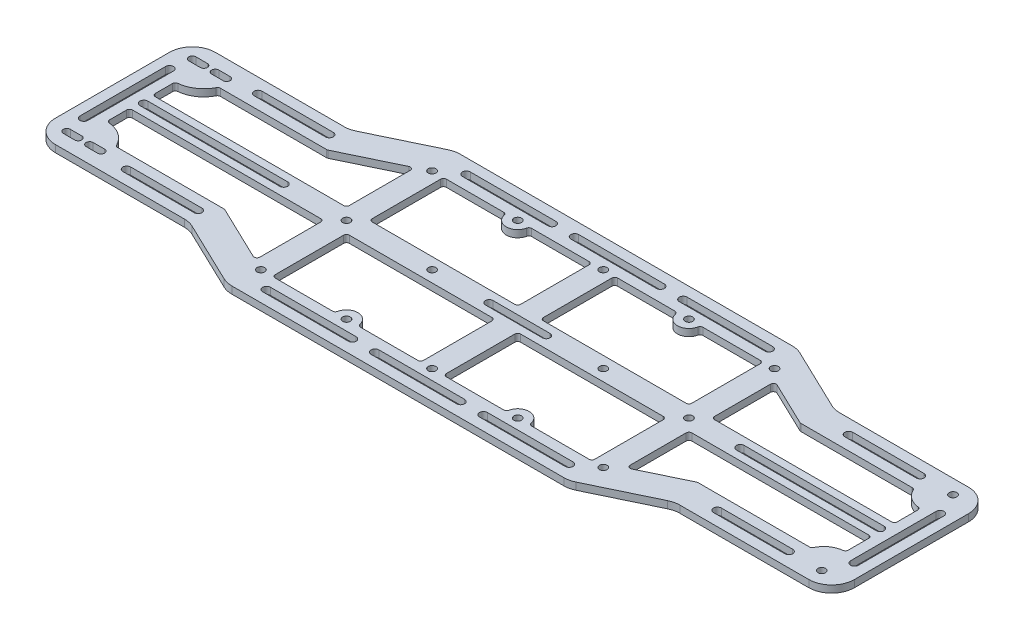
SolidWorks part; units mm, degrees
material "6061-T6 (SS)"
ref_plane "Front Plane" through (0, 0, 0) normal (0, 0, 1) x (1, 0, 0)
ref_plane "Top Plane" through (0, 0, 0) normal (0, 1, 0) x (1, 0, 0)
ref_plane "Right Plane" through (0, 0, 0) normal (1, 0, 0) x (0, 0, -1)
sketch "Sketch1" plane through (0, 0, 0) normal (0, 1, 0) x (1, 0, 0)
  line L1 (0, 0) -> (355.6, 0)
  line L2 (0, 0) -> (0, 101.6)
  line L3 (0, 101.6) -> (355.6, 101.6)
  line L4 (355.6, 0) -> (355.6, 101.6)
  dimension "D1" = 355.6
  dimension "D2" = 101.6
extrude "Boss-Extrude1" add sketch "Sketch1" along normal blind 3.175
sketch "Sketch2" plane through (0, 0, 0) normal (0, -1, 0) x (1, 0, 0)
  line L0 (0, -50.8) -> (355.6, -50.8) construction
  line L1 (0, -101.6) -> (0, 0) construction
  line L2 (355.6, 0) -> (355.6, -101.6) construction
  point P6 (10.16, -22.86)
  point P7 (344.8634, -21.59)
  point P8 (344.8634, -80.01)
  point P9 (10.16, -78.74)
  dimension "D1" = 55.88
  dimension "D2" = 58.42
  dimension "D3" = 334.7034
  dimension "D4" = 10.16
hole_wizard "M3 Clearance Hole2" positions "Sketch6" profile "Sketch5" hole size "M3" standard "ANSI Metric" end condition through all
sketch "Sketch6" plane through (0, 0, 0) normal (0, -1, 0) x (-1, 0, 0)
  point P0 (-344.8634, 21.59)
  point P3 (-344.8634, 80.01)
sketch "Sketch5" plane through (344.8634, 0, -21.59) normal (1, 0, 0) x (0, 0, -1)
  line L0 (0, 0) -> (0, 3.175)
  line L1 (0, 3.175) -> (1.7, 3.175)
  line L2 (1.7, 3.175) -> (1.7, 0)
  line L5 (1.7, 0) -> (0, 0)
  line L11 (0, -6.35) -> (0, 107.95) construction
  dimension "Thru Hole Dia." = 3.4
  dimension "Thru Hole Depth" = 3.175
sketch "Sketch7" plane through (0, 0, 0) normal (0, -1, 0) x (1, 0, 0)
  line L0 (7.62, -22.86) -> (12.7, -22.86) construction
  line L1 (7.62, -21.2838) -> (12.7, -21.2838)
  line L2 (7.62, -24.4362) -> (12.7, -24.4362)
  line L3 (0, -50.8) -> (34.1188, -50.8) construction
  line L4 (0, -50.8) -> (355.6, -50.8) construction
  line L5 (7.62, -78.74) -> (12.7, -78.74) construction
  line L6 (7.62, -80.3162) -> (12.7, -80.3162)
  line L7 (7.62, -77.1638) -> (12.7, -77.1638)
  arc A0 (7.62, -21.2838) -> (7.62, -24.4362) centre (7.62, -22.86) ccw
  arc A1 (12.7, -24.4362) -> (12.7, -21.2838) centre (12.7, -22.86) ccw
  arc A2 (7.62, -80.3162) -> (7.62, -77.1638) centre (7.62, -78.74) cw
  arc A3 (12.7, -77.1638) -> (12.7, -80.3162) centre (12.7, -78.74) cw
  point P2 (10.16, -22.86)
  point P15 (10.16, -78.74)
  dimension "D1" = 1.5762
  dimension "D2" = 5.08
extrude "Cut-Extrude1" cut sketch "Sketch7" against normal through all
sketch "Sketch16" plane through (0, 3.175, 0) normal (0, 1, 0) x (1, 0, 0)
  line L0 (355.6, 15.24) -> (285.75, 15.24)
  line L1 (355.6, 0) -> (355.6, 101.6) construction
  line L2 (0, 0) -> (355.6, 0) construction
  line L3 (355.6, 15.24) -> (355.6, 0)
  line L4 (355.6, 0) -> (254, 0)
  line L5 (285.75, 15.24) -> (254, 0)
  line L6 (355.6, 50.8) -> (0, 50.8) construction
  line L7 (0, 101.6) -> (0, 0) construction
  line L8 (177.8, 0) -> (177.8, 101.6) construction
  line L9 (355.6, 101.6) -> (0, 101.6) construction
  line L10 (69.85, 15.24) -> (101.6, 0)
  line L11 (0, 0) -> (101.6, 0)
  line L12 (0, 15.24) -> (0, 0)
  line L13 (0, 15.24) -> (69.85, 15.24)
  line L14 (0, 86.36) -> (69.85, 86.36)
  line L15 (0, 86.36) -> (0, 101.6)
  line L16 (0, 101.6) -> (101.6, 101.6)
  line L17 (69.85, 86.36) -> (101.6, 101.6)
  line L18 (285.75, 86.36) -> (254, 101.6)
  line L19 (355.6, 101.6) -> (254, 101.6)
  line L20 (355.6, 86.36) -> (355.6, 101.6)
  line L21 (355.6, 86.36) -> (285.75, 86.36)
  dimension "D1" = 15.24
  dimension "D2" = 101.6
  dimension "D3" = 69.85
extrude "Cut-Extrude3" cut sketch "Sketch16" against normal through all
fillet "Fillet1" radius 10.16 12 edges at (0, 1.5875, -86.36) (69.85, 1.5875, -86.36) (101.6, 1.5875, -101.6) (254, 1.5875, -101.6) (285.75, 1.5875, -86.36) (355.6, 1.5875, -86.36) (0, 1.5875, -15.24) (69.85, 1.5875, -15.24) (101.6, 1.5875, 0) (254, 1.5875, 0) (285.75, 1.5875, -15.24) (355.6, 1.5875, -15.24)
sketch "Sketch17" plane through (0, 3.175, 0) normal (0, 1, 0) x (1, 0, 0)
  line L0 (0, 50.8) -> (355.6, 50.8) construction
  line L1 (142.24, 88.9) -> (104.14, 50.8) construction
  line L2 (0, 50.8) -> (355.6, 50.8) construction
  line L3 (0, 76.2) -> (0, 25.4) construction
  line L4 (111.76, 88.9) -> (78.74, 55.88)
  line L5 (78.74, 55.88) -> (104.14, 55.88)
  line L6 (104.14, 55.88) -> (137.16, 88.9)
  line L7 (137.16, 88.9) -> (111.76, 88.9)
  line L8 (104.14, 88.9) -> (142.24, 88.9) construction
  line L9 (78.74, 45.72) -> (104.14, 45.72)
  line L10 (104.14, 45.72) -> (137.16, 12.7)
  line L11 (137.16, 12.7) -> (111.76, 12.7)
  line L12 (111.76, 12.7) -> (78.74, 45.72)
  line L13 (175.26, 88.9) -> (149.86, 88.9)
  line L14 (149.86, 88.9) -> (116.84, 55.88)
  line L15 (142.24, 55.88) -> (175.26, 88.9)
  line L16 (116.84, 55.88) -> (142.24, 55.88)
  line L17 (116.84, 45.72) -> (142.24, 45.72)
  line L18 (142.24, 45.72) -> (175.26, 12.7)
  line L19 (149.86, 12.7) -> (116.84, 45.72)
  line L20 (175.26, 12.7) -> (149.86, 12.7)
  line L21 (213.36, 88.9) -> (187.96, 88.9)
  line L22 (187.96, 88.9) -> (154.94, 55.88)
  line L23 (180.34, 55.88) -> (213.36, 88.9)
  line L24 (154.94, 55.88) -> (180.34, 55.88)
  line L25 (154.94, 45.72) -> (180.34, 45.72)
  line L26 (180.34, 45.72) -> (213.36, 12.7)
  line L27 (187.96, 12.7) -> (154.94, 45.72)
  line L28 (213.36, 12.7) -> (187.96, 12.7)
  line L29 (251.46, 88.9) -> (226.06, 88.9)
  line L30 (226.06, 88.9) -> (193.04, 55.88)
  line L31 (218.44, 55.88) -> (251.46, 88.9)
  line L32 (193.04, 55.88) -> (218.44, 55.88)
  line L33 (193.04, 45.72) -> (218.44, 45.72)
  line L34 (218.44, 45.72) -> (251.46, 12.7)
  line L35 (226.06, 12.7) -> (193.04, 45.72)
  line L36 (251.46, 12.7) -> (226.06, 12.7)
  line L37 (260.0411, 84.7811) -> (231.14, 55.88)
  line L38 (231.14, 55.88) -> (256.54, 55.88)
  line L39 (256.54, 55.88) -> (277.2032, 76.5432)
  line L40 (277.2032, 76.5432) -> (260.0411, 84.7811)
  line L41 (256.0844, 100.5995) -> (283.6656, 87.3605) construction
  line L42 (231.14, 45.72) -> (256.54, 45.72)
  line L43 (260.0411, 16.8189) -> (231.14, 45.72)
  line L44 (256.54, 45.72) -> (277.2032, 25.0568)
  line L45 (277.2032, 25.0568) -> (260.0411, 16.8189)
  line L46 (287.02, 73.66) -> (269.24, 55.88)
  line L47 (269.24, 55.88) -> (342.9, 55.88)
  line L48 (342.9, 55.88) -> (342.9, 67.4627)
  line L49 (287.02, 73.66) -> (333.8649, 73.66)
  line L51 (288.0621, 86.36) -> (345.44, 86.36) construction
  line L52 (355.6, 25.4) -> (355.6, 76.2) construction
  line L53 (269.24, 45.72) -> (342.9, 45.72)
  line L54 (342.9, 45.72) -> (342.9, 34.1373)
  line L55 (287.02, 27.94) -> (333.8649, 27.94)
  line L56 (287.02, 27.94) -> (269.24, 45.72)
  line L57 (12.7, 55.88) -> (66.04, 55.88)
  line L58 (66.04, 55.88) -> (86.36, 76.2)
  line L59 (72.7401, 73.66) -> (24.3397, 73.66)
  line L60 (12.7, 66.04) -> (12.7, 55.88)
  line L61 (10.16, 86.36) -> (67.5379, 86.36) construction
  line L62 (86.36, 76.2) -> (94.0476, 83.8876)
  line L63 (94.0476, 83.8876) -> (72.7401, 73.66)
  line L64 (71.9344, 87.3605) -> (99.5156, 100.5995) construction
  line L65 (12.7, 45.72) -> (66.04, 45.72)
  line L66 (86.36, 25.4) -> (94.0476, 17.7124)
  line L67 (66.04, 45.72) -> (86.36, 25.4)
  line L68 (94.0476, 17.7124) -> (72.7401, 27.94)
  line L69 (72.7401, 27.94) -> (24.3397, 27.94)
  line L70 (12.7, 35.56) -> (12.7, 45.72)
  arc A0 (342.9, 67.4627) -> (333.8649, 73.66) centre (344.8634, 80.01) cw
  circle A1 centre (344.8634, 80.01) radius 1.7 construction
  arc A2 (342.9, 34.1373) -> (333.8649, 27.94) centre (344.8634, 21.59) ccw
  arc A3 (24.3397, 73.66) -> (12.7, 66.04) centre (12.7, 78.74) cw
  arc A4 (12.7, 77.1638) -> (12.7, 80.3162) centre (12.7, 78.74) ccw construction
  arc A5 (24.3397, 27.94) -> (12.7, 35.56) centre (12.7, 22.86) ccw
  point P4 (104.14, 88.9)
  point P8 (104.14, 50.8)
  point P9 (104.14, 12.7)
  point P12 (142.24, 88.9)
  point P13 (142.24, 50.8)
  point P14 (142.24, 12.7)
  point P15 (180.34, 88.9)
  point P16 (180.34, 50.8)
  point P17 (180.34, 12.7)
  point P18 (218.44, 88.9)
  point P19 (218.44, 50.8)
  point P20 (218.44, 12.7)
  point P21 (256.54, 88.9)
  point P22 (256.54, 50.8)
  point P23 (256.54, 12.7)
  dimension "D13" = 12.7
  dimension "D17" = 12.7
  dimension "D1" = 38.1
  dimension "D2" = 104.14
  dimension "D4" = 45
  dimension "D5" = 5.08
  dimension "D6" = 25.4
  dimension "D7" = 7.62
  dimension "D9" = 38.1
  dimension "D10" = 38.1
  dimension "D11" = 12.7
  dimension "D12" = 12.7
  dimension "D14" = 12.7
  dimension "D15" = 12.7
  dimension "D16" = 38.1
  dimension "D18" = 12.7
  dimension "D19" = 38.1
  dimension "D3" = 5
  dimension "D8" = 4
hole_wizard "M3 Clearance Hole5" positions "Sketch19" profile "Sketch18" hole size "M3" standard "ANSI Metric" end condition through all
sketch "Sketch19" plane through (0, 3.175, 0) normal (0, 1, 0) x (1, 0, 0)
  point P0 (104.14, 88.9)
  point P3 (142.24, 88.9)
  point P6 (180.34, 88.9)
  point P9 (218.44, 88.9)
  point P12 (256.54, 88.9)
  point P15 (256.54, 12.7)
  point P18 (218.44, 12.7)
  point P21 (180.34, 12.7)
  point P24 (142.24, 12.7)
  point P27 (104.14, 12.7)
  point P30 (104.14, 50.8)
  point P33 (256.54, 50.8)
  point P36 (142.24, 50.8)
  point P39 (180.34, 50.8)
  point P42 (218.44, 50.8)
sketch "Sketch18" plane through (104.14, 3.175, -88.9) normal (1, 0, 0) x (0, 0, 1)
  line L0 (0, 0) -> (0, 3.175)
  line L1 (0, 3.175) -> (1.7, 3.175)
  line L2 (1.7, 3.175) -> (1.7, 0)
  line L5 (1.7, 0) -> (0, 0)
  line L11 (0, -6.35) -> (0, 107.95) construction
  dimension "Thru Hole Dia." = 3.4
  dimension "Thru Hole Depth" = 3.175
sketch "Sketch20" plane through (0, 3.175, 0) normal (0, 1, 0) x (1, 0, 0)
  line L0 (167.64, 50.8) -> (193.04, 50.8) construction
  line L1 (0, 50.8) -> (355.6, 50.8) construction
  line L2 (167.64, 52.5) -> (193.04, 52.5)
  line L3 (167.64, 49.1) -> (193.04, 49.1)
  arc A0 (167.64, 52.5) -> (167.64, 49.1) centre (167.64, 50.8) ccw
  arc A1 (193.04, 49.1) -> (193.04, 52.5) centre (193.04, 50.8) ccw
  circle A2 centre (180.34, 50.8) radius 1.7 construction
  point P5 (180.34, 50.8)
  dimension "D1" = 25.4
extrude "Cut-Extrude5" cut sketch "Sketch20" against normal through all
pattern_linear "LPattern1" count 2 spacing 10.16 along (1, 0, 0) of "Cut-Extrude1"
sketch "Sketch22" plane through (0, 3.175, 0) normal (0, 1, 0) x (1, 0, 0)
  line L0 (13.97, 50.8) -> (76.2, 50.8) construction
  line L1 (0, 50.8) -> (355.6, 50.8) construction
  line L2 (13.97, 52.55) -> (76.2, 52.55)
  line L3 (13.97, 49.05) -> (76.2, 49.05)
  line L4 (0, 76.2) -> (0, 25.4) construction
  arc A0 (13.97, 52.55) -> (13.97, 49.05) centre (13.97, 50.8) ccw
  arc A1 (76.2, 49.05) -> (76.2, 52.55) centre (76.2, 50.8) ccw
  point P4 (45.085, 50.8)
  dimension "D3" = 76.2
  dimension "D1" = 3.5
  dimension "D2" = 13.97
extrude "Cut-Extrude6" cut sketch "Sketch22" against normal through all
sketch "Sketch23" plane through (0, 3.175, 0) normal (0, 1, 0) x (1, 0, 0)
  line L0 (279.4, 50.8) -> (341.63, 50.8) construction
  line L1 (0, 50.8) -> (355.6, 50.8) construction
  line L2 (279.4, 52.55) -> (341.63, 52.55)
  line L3 (279.4, 49.05) -> (341.63, 49.05)
  line L4 (355.6, 25.4) -> (355.6, 76.2) construction
  arc A0 (279.4, 52.55) -> (279.4, 49.05) centre (279.4, 50.8) ccw
  arc A1 (341.63, 49.05) -> (341.63, 52.55) centre (341.63, 50.8) ccw
  point P4 (310.515, 50.8)
  dimension "D2" = 13.97
  dimension "D3" = 76.2
  dimension "D1" = 3.5
extrude "Cut-Extrude7" cut sketch "Sketch23" against normal through all
sketch "Sketch24" plane through (0, 3.175, 0) normal (0, 1, 0) x (1, 0, 0)
  line L0 (6.35, 69.85) -> (6.35, 31.75) construction
  line L1 (0, 50.8) -> (355.6, 50.8) construction
  line L2 (8.1, 69.85) -> (8.1, 31.75)
  line L3 (4.6, 69.85) -> (4.6, 31.75)
  line L4 (349.25, 69.85) -> (349.25, 31.75) construction
  line L5 (351, 69.85) -> (351, 31.75)
  line L6 (347.5, 69.85) -> (347.5, 31.75)
  line L7 (0, 76.2) -> (0, 25.4) construction
  line L8 (355.6, 25.4) -> (355.6, 76.2) construction
  arc A0 (8.1, 69.85) -> (4.6, 69.85) centre (6.35, 69.85) ccw
  arc A1 (4.6, 31.75) -> (8.1, 31.75) centre (6.35, 31.75) ccw
  arc A2 (351, 69.85) -> (347.5, 69.85) centre (349.25, 69.85) ccw
  arc A3 (347.5, 31.75) -> (351, 31.75) centre (349.25, 31.75) ccw
  point P4 (6.35, 50.8)
  point P10 (349.25, 50.8)
  dimension "D1" = 3.5
  dimension "D2" = 38.1
  dimension "D3" = 6.35
  dimension "D4" = 6.35
extrude "Cut-Extrude8" cut sketch "Sketch24" against normal through all
sketch "Sketch25" plane through (0, 3.175, 0) normal (0, 1, 0) x (1, 0, 0)
  line L0 (101.3472, 95.25) -> (256.2857, 95.25) construction
  line L1 (251.6879, 101.6) -> (103.9121, 101.6) construction
  line L2 (113.03, 95.25) -> (151.13, 95.25) construction
  line L3 (113.03, 97) -> (151.13, 97)
  line L4 (113.03, 93.5) -> (151.13, 93.5)
  line L5 (161.29, 95.25) -> (199.39, 95.25) construction
  line L6 (161.29, 97) -> (199.39, 97)
  line L7 (161.29, 93.5) -> (199.39, 93.5)
  line L8 (209.55, 95.25) -> (247.65, 95.25) construction
  line L9 (209.55, 97) -> (247.65, 97)
  line L10 (209.55, 93.5) -> (247.65, 93.5)
  line L11 (0, 76.2) -> (0, 25.4) construction
  arc A0 (113.03, 97) -> (113.03, 93.5) centre (113.03, 95.25) ccw
  arc A1 (151.13, 93.5) -> (151.13, 97) centre (151.13, 95.25) ccw
  arc A2 (161.29, 97) -> (161.29, 93.5) centre (161.29, 95.25) ccw
  arc A3 (199.39, 93.5) -> (199.39, 97) centre (199.39, 95.25) ccw
  arc A4 (209.55, 97) -> (209.55, 93.5) centre (209.55, 95.25) ccw
  arc A5 (247.65, 93.5) -> (247.65, 97) centre (247.65, 95.25) ccw
  point P6 (132.08, 95.25)
  point P11 (180.34, 95.25)
  point P18 (228.6, 95.25)
  dimension "D3" = 10.16
  dimension "D4" = 10.16
  dimension "D5" = 113.03
  dimension "D1" = 6.35
  dimension "D2" = 38.1
  dimension "D6" = 3.5
extrude "Cut-Extrude9" cut sketch "Sketch25" against normal through all
ref_plane "Plane1" through (0, 0, -50.8) normal (0, 0, -1) x (-1, 0, 0)
mirror "Mirror1" about plane through (0, 0, -50.8) normal (0, 0, -1) of "Cut-Extrude9"
sketch "Sketch26" plane through (0, 3.175, 0) normal (0, 1, 0) x (1, 0, 0)
  line L0 (26.8574, 80.01) -> (337.2378, 80.01) construction
  line L1 (35.56, 80.01) -> (67.31, 80.01) construction
  line L2 (35.56, 81.76) -> (67.31, 81.76)
  line L3 (35.56, 78.26) -> (67.31, 78.26)
  line L4 (298.45, 80.01) -> (330.2, 80.01) construction
  line L5 (298.45, 81.76) -> (330.2, 81.76)
  line L6 (298.45, 78.26) -> (330.2, 78.26)
  line L7 (10.16, 86.36) -> (67.5379, 86.36) construction
  line L8 (0, 76.2) -> (0, 25.4) construction
  line L9 (355.6, 25.4) -> (355.6, 76.2) construction
  arc A0 (35.56, 81.76) -> (35.56, 78.26) centre (35.56, 80.01) ccw
  arc A1 (67.31, 78.26) -> (67.31, 81.76) centre (67.31, 80.01) ccw
  arc A2 (298.45, 81.76) -> (298.45, 78.26) centre (298.45, 80.01) ccw
  arc A3 (330.2, 78.26) -> (330.2, 81.76) centre (330.2, 80.01) ccw
  point P4 (51.435, 80.01)
  point P9 (314.325, 80.01)
  dimension "D4" = 35.56
  dimension "D5" = 25.4
  dimension "D1" = 31.75
  dimension "D2" = 3.5
  dimension "D3" = 6.35
extrude "Cut-Extrude10" cut sketch "Sketch26" against normal through all
mirror "Mirror2" about plane through (0, 0, -50.8) normal (0, 0, -1) of "Cut-Extrude10"
sketch "Sketch28" plane through (0, 3.175, 0) normal (0, 1, 0) x (1, 0, 0)
  line L0 (12.7, 55.88) -> (12.7, 66.04)
  line L1 (24.3397, 73.66) -> (72.7401, 73.66)
  line L2 (72.7401, 73.66) -> (99.06, 86.2935)
  line L3 (99.06, 86.2935) -> (99.06, 55.88)
  line L4 (78.74, 55.88) -> (104.14, 55.88) construction
  line L5 (99.06, 55.88) -> (12.7, 55.88)
  line L6 (109.22, 88.9) -> (109.22, 55.88)
  line L7 (137.16, 88.9) -> (111.76, 88.9) construction
  line L8 (109.22, 55.88) -> (175.26, 55.88)
  line L9 (154.94, 55.88) -> (180.34, 55.88) construction
  line L10 (175.26, 55.88) -> (175.26, 88.9)
  line L11 (175.26, 88.9) -> (149.86, 88.9) construction
  line L12 (175.26, 88.9) -> (147.32, 88.9)
  line L13 (137.16, 88.9) -> (109.22, 88.9)
  line L14 (185.42, 88.9) -> (185.42, 55.88)
  line L15 (213.36, 88.9) -> (187.96, 88.9) construction
  line L16 (185.42, 55.88) -> (251.46, 55.88)
  line L17 (231.14, 55.88) -> (256.54, 55.88) construction
  line L18 (251.46, 55.88) -> (251.46, 88.9)
  line L19 (251.46, 88.9) -> (226.06, 88.9) construction
  line L20 (251.46, 88.9) -> (223.52, 88.9)
  line L21 (213.36, 88.9) -> (185.42, 88.9)
  line L22 (342.9, 55.88) -> (342.9, 67.4627)
  line L23 (333.8649, 73.66) -> (287.02, 73.66)
  line L24 (283.21, 73.66) -> (261.62, 84.0232)
  line L25 (277.2032, 76.5432) -> (260.0411, 84.7811) construction
  line L26 (261.62, 84.0232) -> (261.62, 55.88)
  line L27 (261.62, 55.88) -> (342.9, 55.88)
  line L28 (287.02, 73.66) -> (283.21, 73.66)
  arc A0 (12.7, 66.04) -> (24.3397, 73.66) centre (12.7, 78.74) ccw
  arc A1 (147.32, 88.9) -> (137.16, 88.9) centre (142.24, 88.9) cw
  arc A2 (223.52, 88.9) -> (213.36, 88.9) centre (218.44, 88.9) cw
  arc A3 (342.9, 67.4627) -> (333.8649, 73.66) centre (342.9, 77.1475) cw
  dimension "D5" = 5.08
  dimension "D6" = 5.08
  dimension "D1" = 5.08
  dimension "D2" = 5.08
  dimension "D3" = 5.08
  dimension "D4" = 5.08
  dimension "D7" = 5.08
  dimension "D8" = 5.08
extrude "Cut-Extrude11" cut sketch "Sketch28" against normal through all
fillet "Fillet2" radius 1.27 2 edges at (261.62, 1.5875, -84.0232) (99.06, 1.5875, -86.2935)
fillet "Fillet3" radius 1.27 5 edges at (12.7, 1.5875, -55.88) (99.06, 1.5875, -55.88) (72.7401, 1.5875, -73.66) (12.7, 1.5875, -66.04) (24.3397, 1.5875, -73.66)
fillet "Fillet4" radius 1.27 12 edges at (185.42, 1.5875, -55.88) (251.46, 1.5875, -55.88) (251.46, 1.5875, -88.9) (213.36, 1.5875, -88.9) (223.52, 1.5875, -88.9) (185.42, 1.5875, -88.9) (109.22, 1.5875, -88.9) (147.32, 1.5875, -88.9) (137.16, 1.5875, -88.9) (175.26, 1.5875, -88.9) (175.26, 1.5875, -55.88) (109.22, 1.5875, -55.88)
fillet "Fillet5" radius 1.27 5 edges at (283.21, 1.5875, -73.66) (333.8649, 1.5875, -73.66) (342.9, 1.5875, -67.4627) (342.9, 1.5875, -55.88) (261.62, 1.5875, -55.88)
mirror "Mirror3" about plane through (0, 0, -50.8) normal (0, 0, -1) of "Fillet5", "Fillet4", "Fillet3", "Fillet2", "Cut-Extrude11"
